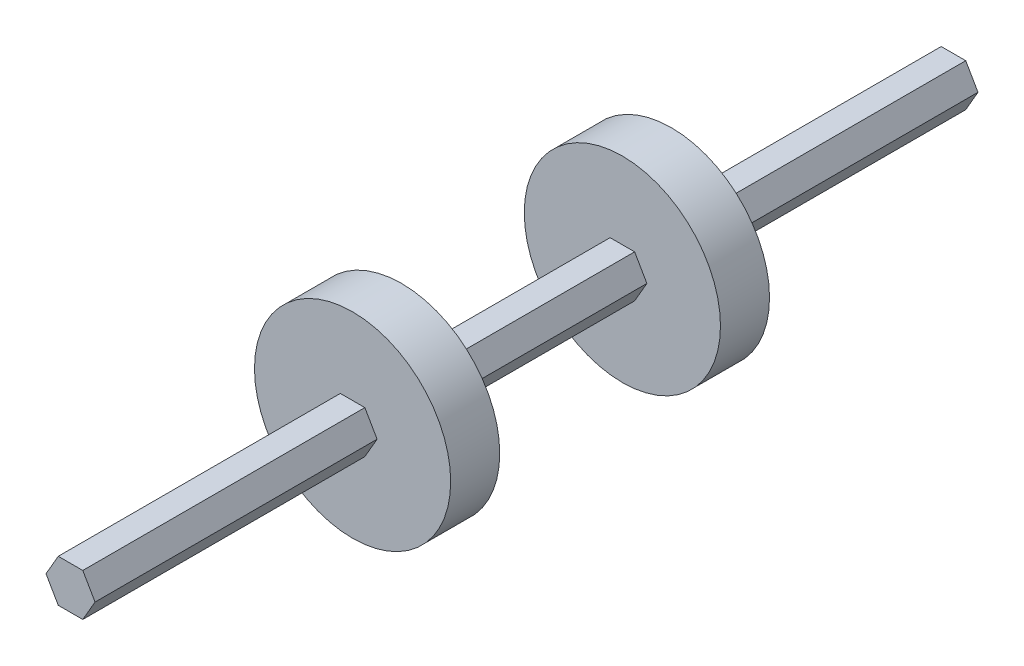
SolidWorks part; units mm, degrees
ref_plane "Front Plane" through (0, 0, 0) normal (0, 0, 1) x (1, 0, 0)
ref_plane "Top Plane" through (0, 0, 0) normal (0, 1, 0) x (1, 0, 0)
ref_plane "Right Plane" through (0, 0, 0) normal (1, 0, 0) x (0, 0, -1)
sketch "Sketch1" plane through (0, 0, 0) normal (0, 0, 1) x (1, 0, 0)
  line L1 (-3.175, 5.4993) -> (-6.35, 0)
  line L2 (-6.35, 0) -> (-3.175, -5.4993)
  line L3 (-3.175, -5.4993) -> (3.175, -5.4993)
  line L4 (3.175, -5.4993) -> (6.35, 0)
  line L5 (6.35, 0) -> (3.175, 5.4993)
  line L6 (3.175, 5.4993) -> (-3.175, 5.4993)
  circle A0 centre (0, 0) radius 5.4993 construction
  dimension "D1" = 12.7
extrude "Boss-Extrude1" add sketch "Sketch1" along normal blind 228.6
ref_plane "Plane1" through (0, 0, 114.3) normal (0, 0, 1) x (1, 0, 0)
ref_plane "Plane2" through (0, 0, 85.725) normal (0, 0, 1) x (1, 0, 0)
ref_plane "Plane3" through (0, 0, 142.875) normal (0, 0, 1) x (1, 0, 0)
sketch "Sketch2" plane through (0, 0, 85.725) normal (0, 0, 1) x (1, 0, 0)
  circle A0 centre (0, 0) radius 25.4
  dimension "D1" = 50.8
sketch "Sketch3" plane through (0, 0, 142.875) normal (0, 0, 1) x (1, 0, 0)
  circle A0 centre (0, 0) radius 25.4 construction
  circle A1 centre (0, 0) radius 25.4
extrude "Boss-Extrude2" add sketch "Sketch2" against normal blind 12.7
extrude "Boss-Extrude3" add sketch "Sketch3" along normal blind 12.7
